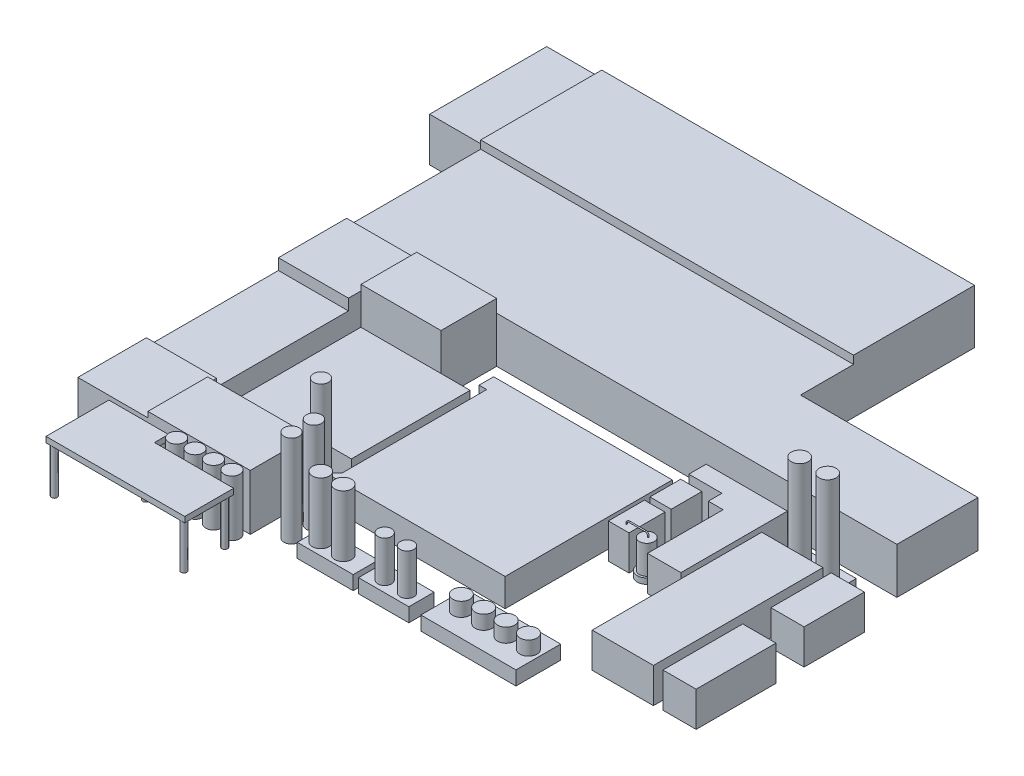
SolidWorks part; units mm, degrees
ref_plane "Front Plane" through (0, 0, 0) normal (0, 0, 1) x (1, 0, 0)
ref_plane "Top Plane" through (0, 0, 0) normal (0, 1, 0) x (1, 0, 0)
ref_plane "Right Plane" through (0, 0, 0) normal (1, 0, 0) x (0, 0, -1)
sketch "Sketch1" plane through (0, 0, 0) normal (0, 1, 0) x (1, 0, 0)
  line L1 (0, 0) -> (-10.36, 0)
  line L2 (0, 0) -> (0, -20.93)
  line L3 (0, -20.93) -> (-10.36, -20.93)
  line L4 (-10.36, 0) -> (-10.36, -20.93)
  dimension "D1" = 10.36
  dimension "D2" = 20.93
extrude "Boss-Extrude1" add sketch "Sketch1" along normal blind 7.85
sketch "Sketch2" plane through (0, 0, 0) normal (0, 1, 0) x (1, 0, 0)
  line L0 (0, -20.93) -> (0, 0) construction
  line L1 (0, -0.5216) -> (66.62, -0.5216)
  line L2 (0, -0.5216) -> (0, -22.1516)
  line L3 (0, -22.1516) -> (66.62, -22.1516)
  line L4 (66.62, -0.5216) -> (66.62, -22.1516)
  dimension "D1" = 66.62
  dimension "D2" = 21.63
extrude "Boss-Extrude2" add sketch "Sketch2" along normal blind 9.66
sketch "Sketch3" plane through (0, 0, 0) normal (0, 1, 0) x (1, 0, 0)
  line L0 (0, -22.1516) -> (0, -46.1116)
  line L1 (0, -46.1116) -> (98.34, -46.1116)
  line L2 (98.34, -46.1116) -> (98.34, -31.6216)
  line L3 (98.34, -31.6216) -> (68.8641, -31.6216)
  line L5 (0, -22.1516) -> (66.62, -22.1516)
  line L6 (66.62, -22.1516) -> (66.62, -31.6216)
  line L7 (66.62, -31.6216) -> (68.8641, -31.6216)
  dimension "D1" = 23.96
  dimension "D2" = 14.49
  dimension "D3" = 29.4759
  dimension "D4" = 98.34
extrude "Boss-Extrude3" add sketch "Sketch3" along normal blind 8.22
sketch "Sketch4" plane through (0, 0, 0) normal (0, 1, 0) x (1, 0, 0)
  line L1 (0, -46.1116) -> (12.52, -46.1116)
  line L2 (0, -46.1116) -> (0, -58.3116)
  line L3 (0, -58.3116) -> (12.52, -58.3116)
  line L4 (12.52, -46.1116) -> (12.52, -58.3116)
  dimension "D1" = 12.2
  dimension "D2" = 12.52
extrude "Boss-Extrude4" add sketch "Sketch4" along normal blind 9.51
sketch "Sketch5" plane through (0, 0, 0) normal (0, 1, 0) x (1, 0, 0)
  line L1 (12.52, -46.1116) -> (26.81, -46.1116)
  line L2 (12.52, -46.1116) -> (12.52, -56.0616)
  line L3 (12.52, -56.0616) -> (26.81, -56.0616)
  line L4 (26.81, -46.1116) -> (26.81, -56.0616)
  dimension "D1" = 9.95
  dimension "D2" = 14.29
extrude "Boss-Extrude5" add sketch "Sketch5" along normal blind 10.52
sketch "Sketch6" plane through (0, 0, 0) normal (0, 1, 0) x (1, 0, 0)
  line L1 (0, -58.3116) -> (12.52, -58.3116)
  line L2 (0, -58.3116) -> (0, -81.8916)
  line L3 (0, -81.8916) -> (12.52, -81.8916)
  line L4 (12.52, -58.3116) -> (12.52, -81.8916)
  dimension "D1" = 23.58
  dimension "D2" = 12.52
extrude "Boss-Extrude6" add sketch "Sketch6" along normal blind 7.53
sketch "Sketch7" plane through (0, 0, 0) normal (0, 1, 0) x (1, 0, 0)
  line L1 (0, -81.8916) -> (12.52, -81.8916)
  line L2 (0, -81.8916) -> (0, -94.1516)
  line L3 (0, -94.1516) -> (12.52, -94.1516)
  line L4 (12.52, -81.8916) -> (12.52, -94.1516)
  dimension "D1" = 12.52
  dimension "D2" = 12.26
extrude "Boss-Extrude7" add sketch "Sketch7" along normal blind 8.91
sketch "Sketch8" plane through (0, 0, 0) normal (0, 1, 0) x (1, 0, 0)
  line L1 (12.52, -94.1516) -> (30.81, -94.1516)
  line L2 (12.52, -94.1516) -> (12.52, -83.4716)
  line L3 (12.52, -83.4716) -> (30.81, -83.4716)
  line L4 (30.81, -94.1516) -> (30.81, -83.4716)
  dimension "D1" = 10.68
  dimension "D2" = 18.29
extrude "Boss-Extrude8" add sketch "Sketch8" along normal blind 9.91
sketch "Sketch10" plane through (0, 0, 0) normal (0, 1, 0) x (1, 0, 0)
  circle A0 centre (35.0337, -87.0012) radius 1.345
  circle A1 centre (35.0337, -91.0012) radius 1.345
  dimension "D1" = 2.69
  dimension "D2" = 2.69
  dimension "D3" = 4
extrude "Boss-Extrude10" add sketch "Sketch10" along normal blind 16.39 separate body
sketch "Sketch11" plane through (0, 0, 0) normal (0, 1, 0) x (1, 0, 0)
  line L1 (38.7202, -89.1612) -> (48.7202, -89.1612)
  line L2 (38.7202, -89.1612) -> (38.7202, -93.6612)
  line L3 (38.7202, -93.6612) -> (48.7202, -93.6612)
  line L4 (48.7202, -89.1612) -> (48.7202, -93.6612)
  line L5 (49.665, -89.1612) -> (58.665, -89.1612)
  line L6 (49.665, -89.1612) -> (49.665, -93.6612)
  line L7 (49.665, -93.6612) -> (58.665, -93.6612)
  line L8 (58.665, -89.1612) -> (58.665, -93.6612)
  dimension "D1" = 9
  dimension "D2" = 10
extrude "Boss-Extrude11" add sketch "Sketch11" along normal blind 2.5 separate body
sketch "Sketch12" plane through (0, 2.5, 0) normal (0, 1, 0) x (1, 0, 0)
  circle A0 centre (40.7646, -91.4906) radius 1.5
  circle A1 centre (44.7646, -91.4906) radius 1.5
  point P4 (0, 0)
  dimension "D1" = 3
  dimension "D2" = 3
  dimension "D3" = 4
extrude "Boss-Extrude12" add sketch "Sketch12" along normal blind 10.94
sketch "Sketch13" plane through (0, 2.5, 0) normal (0, 1, 0) x (1, 0, 0)
  circle A0 centre (52.3668, -91.6834) radius 1.22
  circle A1 centre (56.3668, -91.6834) radius 1.22
  dimension "D1" = 2.44
  dimension "D2" = 2.44
  dimension "D3" = 4
extrude "Boss-Extrude13" add sketch "Sketch13" along normal blind 7.34
sketch "Sketch14" plane through (0, 0, 0) normal (0, 1, 0) x (1, 0, 0)
  line L13 (83.2797, -48.3214) -> (93.2797, -48.3214)
  line L14 (83.2797, -48.3214) -> (83.2797, -53.3214)
  line L15 (83.2797, -53.3214) -> (93.2797, -53.3214)
  line L16 (93.2797, -48.3214) -> (93.2797, -53.3214)
  point P4 (82.5464, -48.6599)
  point P5 (0, 0)
  point P6 (83.2797, -48.3214)
  dimension "D1" = 10
extrude "Boss-Extrude14" add sketch "Sketch14" along normal blind 1.5 separate body
sketch "Sketch15" plane through (0, 1.5, 0) normal (0, 1, 0) x (1, 0, 0)
  line L0 (83.2797, -48.3214) -> (83.2797, -53.3214) construction
  circle A0 centre (85.7797, -50.9316) radius 1.5
  circle A1 centre (90.7797, -50.9316) radius 1.5
  dimension "D2" = 3
  dimension "D3" = 5
  dimension "D6" = 2.5
extrude "Boss-Extrude15" add sketch "Sketch15" along normal blind 16.38
sketch "Sketch16" plane through (0, 0, 0) normal (0, 1, 0) x (1, 0, 0)
  line L1 (82.3984, -54.3309) -> (93.3384, -54.3309)
  line L2 (82.3984, -54.3309) -> (82.3984, -84.6209)
  line L3 (82.3984, -84.6209) -> (93.3384, -84.6209)
  line L4 (93.3384, -54.3309) -> (93.3384, -84.6209)
  line L5 (94.8886, -54.4087) -> (100.8286, -54.4087)
  line L6 (94.8886, -54.4087) -> (94.8886, -65.1887)
  line L7 (94.8886, -65.1887) -> (100.8286, -65.1887)
  line L8 (100.8286, -54.4087) -> (100.8286, -65.1887)
  line L9 (94.8886, -70.2202) -> (100.8286, -70.2202)
  line L10 (94.8886, -70.2202) -> (94.8886, -84.4811)
  line L11 (94.8886, -84.4811) -> (100.8286, -84.4811)
  line L12 (100.8286, -70.2202) -> (100.8286, -84.4811)
  point P12 (82.2571, -84.6209)
  point P13 (94.21, -54.3309)
  point P14 (0, 0)
  point P15 (0, 0)
  point P16 (0, 0)
  point P17 (0, 0)
  point P18 (100.8286, -65.1887)
  dimension "D1" = 10.78
  dimension "D2" = 30.29
  dimension "D3" = 10.94
  dimension "D4" = 5.94
  dimension "D5" = 5.94
extrude "Boss-Extrude16" add sketch "Sketch16" along normal blind 6.23 separate body
sketch "Sketch18" plane through (0, 0, 0) normal (0, 1, 0) x (1, 0, 0)
  line L1 (61.0116, -85.8678) -> (78.0116, -85.8678)
  line L2 (61.0116, -85.8678) -> (61.0116, -93.8678)
  line L3 (61.0116, -93.8678) -> (78.0116, -93.8678)
  line L4 (78.0116, -85.8678) -> (78.0116, -93.8678)
  point P4 (61.0116, -85.8678)
  dimension "D1" = 17
  dimension "D2" = 8
extrude "Boss-Extrude17" add sketch "Sketch18" along normal blind 2.5 separate body
sketch "Sketch19" plane through (0, 2.5, 0) normal (0, 1, 0) x (1, 0, 0)
  circle A0 centre (63.939, -89.5572) radius 1.52
  circle A1 centre (67.939, -89.5572) radius 1.52
  circle A2 centre (71.939, -89.5572) radius 1.52
  circle A3 centre (75.939, -89.5572) radius 1.52
  point P8 (63.939, -89.5572)
  point P9 (69.1848, -89.5572)
  point P10 (74.042, -89.5572)
  point P11 (78.7327, -89.5572)
  point P12 (0, 0)
  point P14 (75.9571, -90.3066)
  dimension "D4" = 3.04
  dimension "D1" = 4
  dimension "D2" = 4
  dimension "D3" = 4
extrude "Boss-Extrude18" add sketch "Sketch19" along normal blind 2.5
sketch "Sketch20" plane through (0, 0, 0) normal (0, 1, 0) x (1, 0, 0)
  line L0 (13.6211, -57.1968) -> (13.6211, -82.071)
  line L1 (13.6211, -82.071) -> (27.7137, -82.071)
  line L2 (27.7137, -82.071) -> (27.7137, -78.4205)
  line L3 (27.7137, -78.4205) -> (33.1469, -78.4205)
  line L4 (33.1469, -78.4205) -> (33.1469, -57.1968)
  line L5 (33.1469, -57.1968) -> (13.6211, -57.1968)
  line L6 (33.1469, -82.8738) -> (65.0818, -82.8738)
  line L7 (65.0818, -82.8738) -> (65.0818, -52.9922)
  line L8 (65.0818, -52.9922) -> (33.1469, -52.9922)
  line L10 (33.1469, -52.9922) -> (33.1469, -55.5939)
  line L11 (33.1469, -55.5939) -> (34.5101, -55.5939)
  line L12 (34.5101, -55.5939) -> (34.5101, -81.4536)
  line L13 (34.5101, -81.4536) -> (33.1469, -82.8738)
extrude "Boss-Extrude19" add sketch "Sketch20" along normal blind 5 separate body
sketch "Sketch21" plane through (0, 0, 0) normal (0, 1, 0) x (1, 0, 0)
  line L1 (28.7918, -79.4464) -> (31.7918, -79.4464)
  line L2 (28.7918, -79.4464) -> (28.7918, -82.4464)
  line L3 (28.7918, -82.4464) -> (31.7918, -82.4464)
  line L4 (31.7918, -79.4464) -> (31.7918, -82.4464)
  point P6 (31.7918, -82.4464)
  dimension "D1" = 3
  dimension "D2" = 3
extrude "Boss-Extrude20" add sketch "Sketch21" along normal blind 1 separate body
sketch "Sketch22" plane through (0, 1, 0) normal (0, 1, 0) x (1, 0, 0)
  line L0 (31.7918, -82.4464) -> (31.7918, -79.4464) construction
  circle A0 centre (30.2918, -80.9894) radius 1.345
  dimension "D1" = 2.69
  dimension "D2" = 1.5
extrude "Boss-Extrude21" add sketch "Sketch22" along normal blind 16.38
sketch "Sketch23" plane through (0, 0, 0) normal (0, 1, 0) x (1, 0, 0)
  line L0 (73.8227, -48.7633) -> (81.4256, -48.7633)
  line L1 (81.4256, -48.7633) -> (81.4256, -67.8005)
  line L2 (81.4256, -67.8005) -> (75.4604, -67.8005)
  line L3 (75.4604, -67.8005) -> (75.4604, -54.2941)
  line L4 (75.4604, -54.2941) -> (72.8148, -54.2941)
  line L5 (72.8148, -54.2941) -> (72.8148, -51.8574)
  line L6 (72.8148, -51.8574) -> (66.8971, -51.8574)
  line L7 (66.8971, -51.8574) -> (66.8971, -48.7633)
  line L8 (66.8971, -48.7633) -> (73.8227, -48.7633)
extrude "Boss-Extrude22" add sketch "Sketch23" along normal blind 6.23 separate body
sketch "Sketch24" plane through (0, 0, 0) normal (0, 1, 0) x (1, 0, 0)
  line L0 (66.9488, -59.8527) -> (70.6333, -59.8527)
  line L1 (66.9488, -53.361) -> (70.7488, -53.361)
  line L2 (66.9488, -53.361) -> (66.9488, -58.861)
  line L3 (66.9488, -58.861) -> (70.7488, -58.861)
  line L4 (70.7488, -53.361) -> (70.7488, -58.861)
  line L5 (66.9488, -59.8527) -> (66.9488, -66.286)
  line L6 (66.9488, -66.286) -> (70.6333, -66.286)
  line L7 (70.6333, -59.8527) -> (70.6333, -66.286)
  point P8 (66.9488, -59.8527)
  point P9 (70.6333, -66.286)
  dimension "D1" = 3.8
  dimension "D2" = 5.5
extrude "Boss-Extrude23" add sketch "Sketch24" along normal blind 6.23 separate body
sketch "Sketch25" plane through (0, 0, 0) normal (0, 1, 0) x (1, 0, 0)
  circle A0 centre (72.7675, -65.2807) radius 1.6719
extrude "Boss-Extrude24" add sketch "Sketch25" along normal blind 1 separate body
sketch "Sketch26" plane through (0, 1, 0) normal (0, 1, 0) x (1, 0, 0)
  circle A0 centre (72.7891, -65.2679) radius 1.32
  dimension "D1" = 2.64
extrude "Boss-Extrude25" add sketch "Sketch26" along normal blind 5.11
sketch3d "3DSketch1"
  line L0 (72.9262, 6.11, 65.1119) -> (72.9262, 6.3028, 65.1119)
  line L1 (72.4262, 6.8028, 65.1119) -> (69.5339, 6.8028, 65.1119)
  line L2 (69.0339, 6.3028, 65.1119) -> (69.0339, 6.0245, 65.1119)
  arc A1 (72.4262, 6.8028, 65.1119) -> (72.9262, 6.3028, 65.1119) centre (72.4262, 6.3028, 65.1119) ccw
  arc A2 (69.5339, 6.8028, 65.1119) -> (69.0339, 6.3028, 65.1119) centre (69.5339, 6.3028, 65.1119) ccw
  point P6 (72.9262, 6.8028, 65.1119)
  point P7 (72.4262, 6.3028, 64.6119)
  point P10 (69.0339, 6.8028, 65.1119)
  point P11 (69.5339, 6.3028, 65.6119)
  dimension "D1" = 0.5
  dimension "D2" = 0.5
sketch "Sketch27" plane through (0, 6.11, 0) normal (0, 1, 0) x (1, 0, 0)
  circle A0 centre (72.9262, -65.1119) radius 0.1
  dimension "D1" = 0.2
sweep "Sweep1" add profiles "Sketch27" path "3DSketch1"
sketch "Sketch30" plane through (0, 0, 0) normal (0, 1, 0) x (1, 0, 0)
  circle A2 centre (7.3352, -94.9795) radius 0.5179
  circle A3 centre (7.3352, -105.6895) radius 0.5179
  circle A5 centre (16.1052, -98.1395) radius 0.5179
  circle A6 centre (30.4852, -98.387) radius 0.5179
  circle A7 centre (30.4894, -105.6895) radius 0.5179
  circle A8 centre (16.1052, -94.9795) radius 0.5179
  point P8 (16.1052, -94.9795)
  dimension "D3" = 3.16
  dimension "D1" = 10.71
  dimension "D2" = 0
  dimension "D4" = 8.77
  dimension "D5" = 14.38
  dimension "D6" = 0
extrude "Boss-Extrude26" add sketch "Sketch30" along normal blind 8 separate body
sketch "Sketch32" plane through (0, 8, 0) normal (0, 1, 0) x (1, 0, 0)
  line L1 (7.3352, -94.9795) -> (16.1052, -94.9795)
  line L6 (7.3352, -94.9795) -> (6.3767, -94.9795)
  line L7 (6.3767, -94.9795) -> (6.3767, -105.6895)
  line L9 (16.1052, -94.9795) -> (17.0219, -94.9795)
  line L10 (17.0219, -94.9795) -> (17.0219, -97.4815)
  line L11 (17.0219, -97.4815) -> (31.1738, -97.4815)
  line L12 (31.1738, -97.4815) -> (31.1738, -106.2169)
  line L13 (31.1738, -106.2169) -> (6.3767, -106.2169)
  line L14 (6.3767, -106.2169) -> (6.3767, -105.6895)
extrude "Boss-Extrude28" add sketch "Sketch32" along normal blind 1
sketch "Sketch33" plane through (0, 0, 0) normal (0, 1, 0) x (1, 0, 0)
  circle A0 centre (19.2531, -95.7601) radius 1.4
  circle A1 centre (22.5531, -95.7601) radius 1.4
  circle A2 centre (25.8531, -95.7601) radius 1.4
  circle A3 centre (29.1531, -95.7601) radius 1.4
  point P8 (0, 0)
  point P9 (0, 0)
  point P10 (29.1618, -95.6692)
  point P11 (0, 0)
  point P12 (0, 0)
  point P13 (0, 0)
  point P14 (36.7978, -100.9871)
  point P15 (29.4345, -95.7601)
  point P16 (0, 0)
  point P17 (0, 0)
  point P18 (0, 0)
  point P19 (0, 0)
  point P20 (0, 0)
  point P22 (0, 0)
  dimension "D1" = 2.8
  dimension "D2" = 3.3
  dimension "D3" = 3.3
  dimension "D4" = 3.3
extrude "Boss-Extrude29" add sketch "Sketch33" along normal blind 10 separate body
